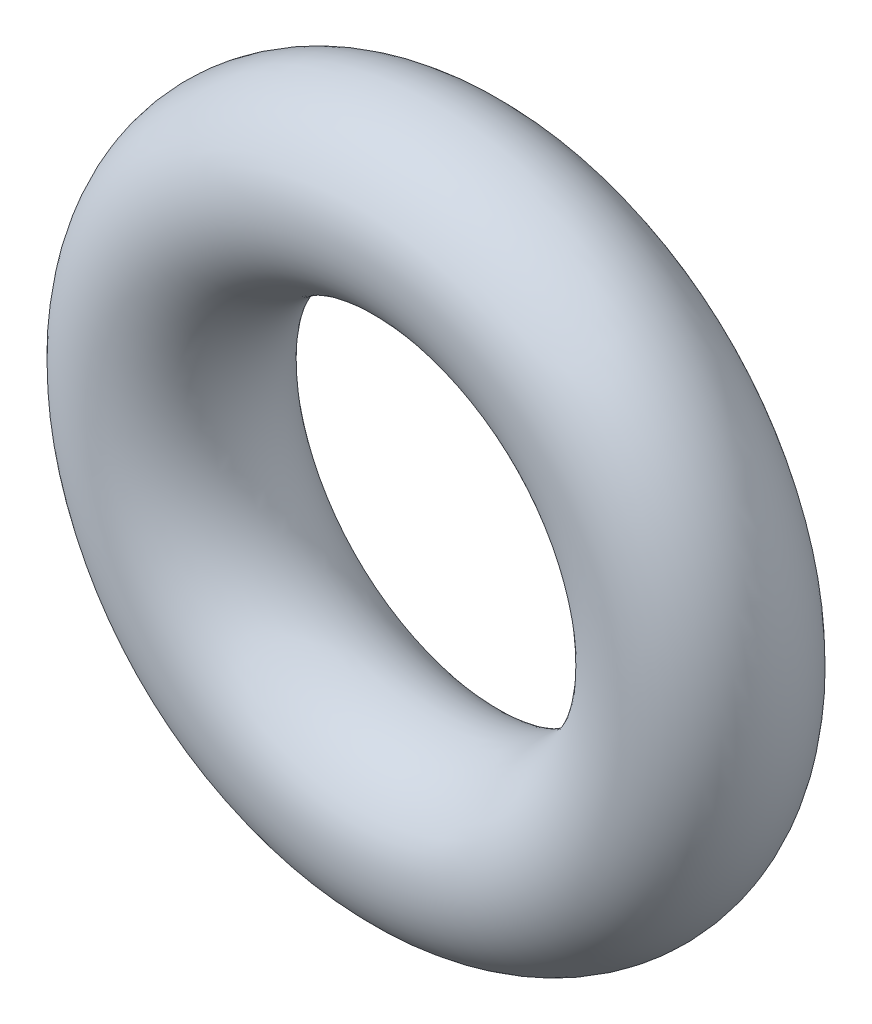
SolidWorks part; units mm, degrees
ref_plane "Front" through (0, 0, 0) normal (0, 0, 1) x (1, 0, 0)
ref_plane "Top" through (0, 0, 0) normal (0, 1, 0) x (1, 0, 0)
ref_plane "Right" through (0, 0, 0) normal (1, 0, 0) x (0, 0, -1)
sketch "Sketch1" plane through (0, 0, 0) normal (1, 0, 0) x (0, -1, 0)
  line L0 (0, -1.3081) -> (0, 1.3081) construction
  line L2 (-5.7556, 0) -> (5.7556, 0) construction
  line L3 (-2.6162, 0) -> (2.6162, 0) construction
  circle A0 centre (3.9243, 0) radius 1.3081
  point P9 (2.6162, 0)
  point P10 (5.2324, 0)
  point P13 (3.9243, 1.3081)
  point P14 (3.9243, -1.3081)
  dimension "Width" = 2.6162
  dimension "ID" = 5.2324
revolve "Revolve1" add sketch "Sketch1" angle 360 about L0
